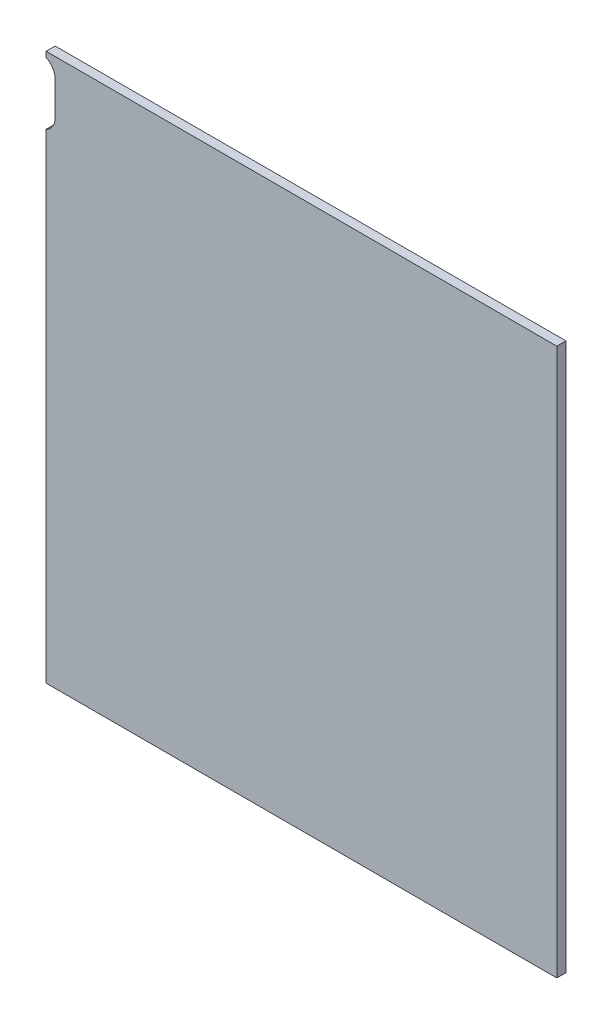
SolidWorks part; units mm, degrees
ref_plane "Front" through (0, 0, 0) normal (0, 0, 1) x (1, 0, 0)
ref_plane "Top" through (0, 0, 0) normal (0, 1, 0) x (1, 0, 0)
ref_plane "Right" through (0, 0, 0) normal (1, 0, 0) x (0, 0, -1)
sketch "Sketch1" plane through (0, 0, 0) normal (0, 0, 1) x (1, 0, 0)
  line L1 (-140, -150) -> (140, -150)
  line L2 (-140, -150) -> (-140, 150)
  line L3 (-140, 150) -> (140, 150)
  line L4 (140, -150) -> (140, 150)
  line L5 (-140, -150) -> (140, 150) construction
  line L6 (-140, 150) -> (140, -150) construction
  point P0 (0, 0)
  dimension "D1" = 300
  dimension "D2" = 280
extrude "Boss-Extrude1" add sketch "Sketch1" along normal blind 5
sketch "Sketch2" plane through (0, 0, 5) normal (0, 0, 1) x (1, 0, 0)
  line L0 (-153, 139) -> (-153, 121)
  line L1 (-135, 139) -> (-135, 121)
  line L2 (-140, 150) -> (-140, -150) construction
  line L3 (140, 150) -> (-140, 150) construction
  arc A0 (-135, 139) -> (-153, 139) centre (-144, 139) ccw
  arc A1 (-153, 121) -> (-135, 121) centre (-144, 121) ccw
  point P1 (-144, 148)
  point P3 (-144, 112)
  dimension "D1" = 9
  dimension "D2" = 9
  dimension "D3" = 36
  dimension "D4" = 4
  dimension "D5" = 2
extrude "Cut-Extrude1" cut sketch "Sketch2" against normal through all
sketch "Sketch3" plane through (0, 0, 0) normal (0, 0, -1) x (-1, 0, 0)
  line L0 (-82.8571, -101.5) -> (-14.4832, -116.5)
  line L1 (-82.8571, -101.5) -> (-85, -111.2677)
  line L2 (-14.4832, -116.5) -> (-16.626, -126.2677)
  line L3 (-85, -111.2677) -> (-16.626, -126.2677)
  line L4 (-140, 150) -> (140, 150) construction
  line L5 (-140, -150) -> (-140, 150) construction
  dimension "D1" = 10
  dimension "D2" = 70
  dimension "D3" = 15
  dimension "D4" = 251.5
  dimension "D5" = 55
extrude "Boss-Extrude2" add sketch "Sketch3" along normal blind 7
sketch "Sketch4" plane through (0, 0, -7) normal (0, 0, -1) x (-1, 0, 0)
  line L0 (-82.8571, -101.5) -> (-14.4832, -116.5)
  line L1 (-82.8571, -101.5) -> (-86.0714, -116.1516)
  line L2 (-14.4832, -116.5) -> (-17.6975, -131.1516)
  line L3 (-86.0714, -116.1516) -> (-17.6975, -131.1516)
  dimension "D1" = 15
extrude "Boss-Extrude3" add sketch "Sketch4" along normal blind 5
